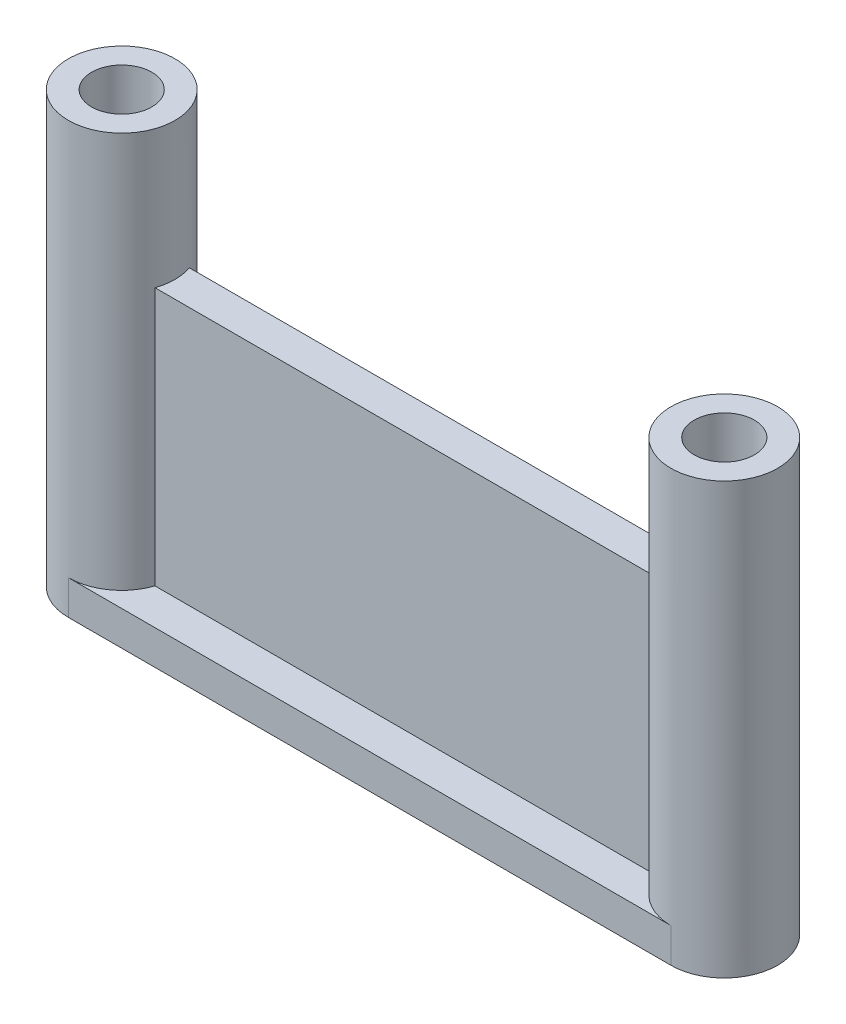
SolidWorks part; units mm, degrees
ref_plane "Спереди" through (0, 0, 0) normal (0, 0, 1) x (1, 0, 0)
ref_plane "Сверху" through (0, 0, 0) normal (0, 1, 0) x (1, 0, 0)
ref_plane "Справа" through (0, 0, 0) normal (1, 0, 0) x (0, 0, -1)
sketch "Эскиз1" plane through (0, 0, 0) normal (0, 1, 0) x (1, 0, 0)
  line L0 (0, 7.9748) -> (0, -9.3328) construction
  circle A0 centre (-17.5, 0) radius 1.75
  circle A1 centre (-17.5, 0) radius 3.1
  circle A2 centre (17.5, 0) radius 3.1
  circle A3 centre (17.5, 0) radius 1.75
  dimension "D1" = 3.5
  dimension "D2" = 6.2
  dimension "D3" = 35
extrude "Бобышка-Вытянуть1" add sketch "Эскиз1" along normal blind 25
sketch "Эскиз2" plane through (0, 0, 0) normal (0, -1, 0) x (1, 0, 0)
  line L0 (-17.5, 3.1) -> (17.5, 3.1)
  line L1 (-17.5, -3.1) -> (17.5, -3.1)
  circle A0 centre (-17.5, 0) radius 3.1 construction
  circle A1 centre (17.5, 0) radius 3.1 construction
  arc A2 (-17.5, 3.1) -> (-17.5, -3.1) centre (-17.5, 0) ccw
  arc A3 (17.5, -3.1) -> (17.5, 3.1) centre (17.5, 0) ccw
  circle A4 centre (-17.5, 0) radius 1.75
  circle A5 centre (17.5, 0) radius 1.75
extrude "Бобышка-Вытянуть2" add sketch "Эскиз2" against normal blind 2
sketch "Эскиз3" plane through (0, 2, 0) normal (0, 1, 0) x (1, 0, 0)
  line L1 (15.088, 1) -> (-15.088, 1)
  line L2 (15.088, 1) -> (15.088, -1)
  line L3 (15.088, -1) -> (-15.088, -1)
  line L4 (-15.088, 1) -> (-15.088, -1)
  line L5 (15.088, 1) -> (-15.088, -1) construction
  line L6 (15.088, -1) -> (-15.088, 1) construction
  point P0 (0, 0)
  dimension "D1" = 2
extrude "Бобышка-Вытянуть3" add sketch "Эскиз3" along normal blind 15
